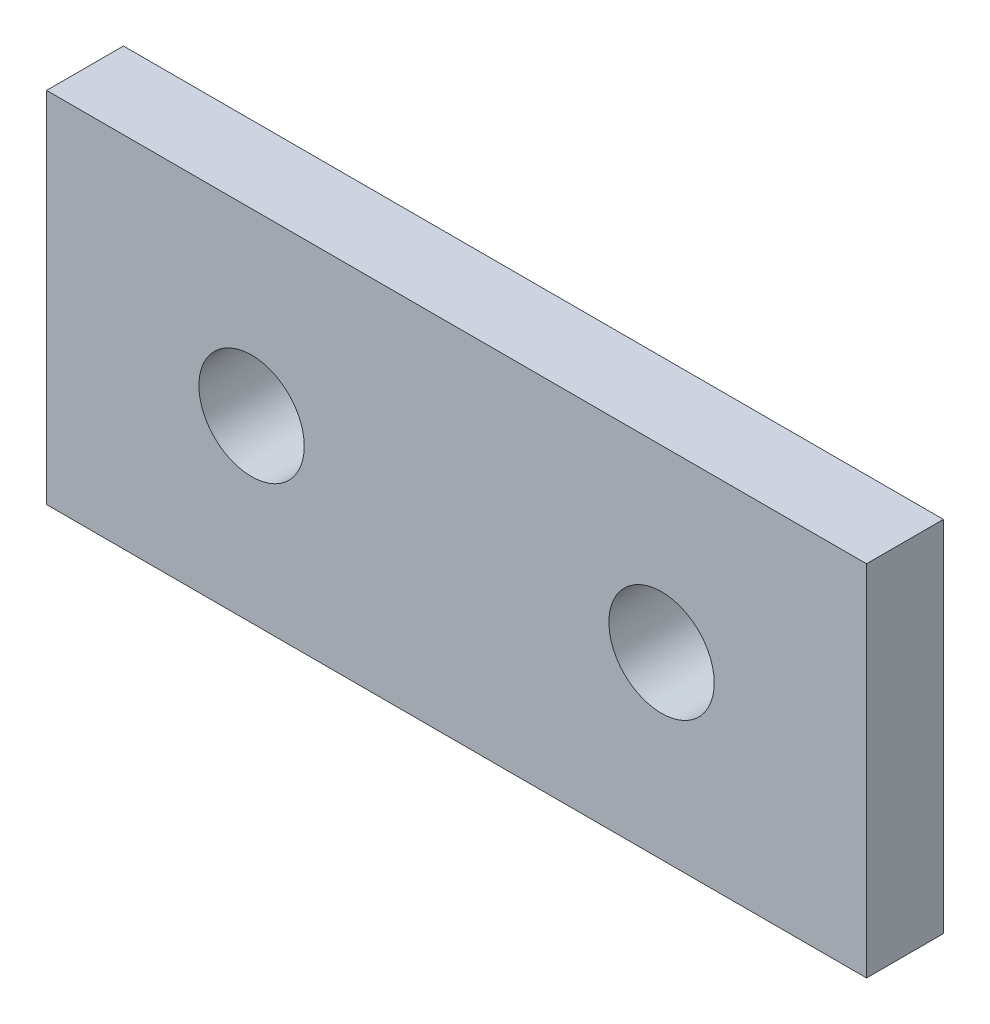
SolidWorks part; units mm, degrees
ref_plane "Front Plane" through (0, 0, 0) normal (0, 0, 1) x (1, 0, 0)
ref_plane "Top Plane" through (0, 0, 0) normal (0, 1, 0) x (1, 0, 0)
ref_plane "Right Plane" through (0, 0, 0) normal (1, 0, 0) x (0, 0, -1)
sketch "Sketch1" plane through (0, 0, 0) normal (0, 0, 1) x (1, 0, 0)
  line L0 (-25.4, -11.1125) -> (25.4, 11.1125) construction
  line L1 (-25.4, 11.1125) -> (25.4, 11.1125)
  line L2 (-25.4, 11.1125) -> (-25.4, -11.1125)
  line L3 (-25.4, -11.1125) -> (25.4, -11.1125)
  line L4 (25.4, 11.1125) -> (25.4, -11.1125)
  line L5 (15.9639, 0) -> (25.4, 0) construction
  line L6 (-15.9639, 0) -> (-25.4, 0) construction
  circle A0 centre (12.7, 0) radius 3.2639
  circle A1 centre (-12.7, 0) radius 3.2639
  dimension "hole" = 6.5278
  dimension "B" = 50.8
  dimension "A" = 22.225
  dimension "center to center" = 25.4
extrude "Extrude1" add sketch "Sketch1" against normal blind 4.7625
mirror "Mirror1" [suppressed]
mirror "Mirror2" [suppressed]
mirror "Mirror4" [suppressed]
